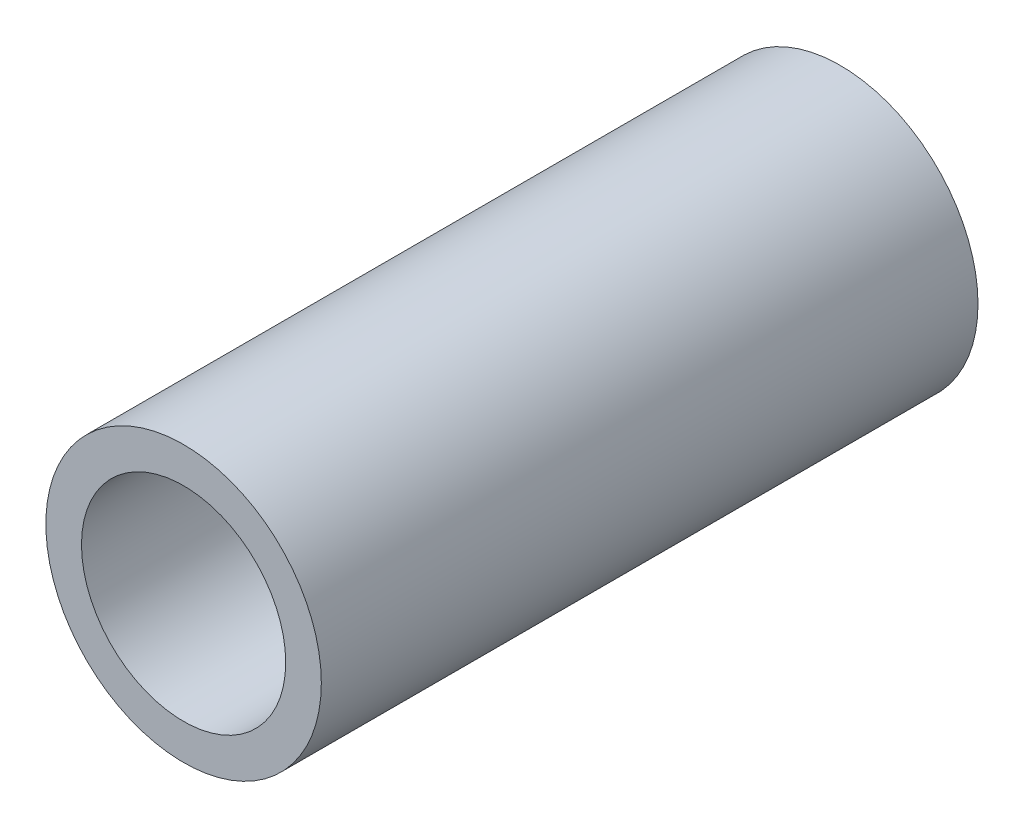
SolidWorks part; units mm, degrees
material "PVC Rigid"
ref_plane "Front Plane" through (0, 0, 0) normal (0, 0, 1) x (1, 0, 0)
ref_plane "Top Plane" through (0, 0, 0) normal (0, 1, 0) x (1, 0, 0)
ref_plane "Right Plane" through (0, 0, 0) normal (1, 0, 0) x (0, 0, -1)
sketch "Sketch1" plane through (0, 0, 0) normal (0, 0, 1) x (1, 0, 0)
  circle A0 centre (0, 0) radius 10.6553
  circle A2 centre (0, 0) radius 7.8994
  dimension "D1" = 21.3106
  dimension "D2" = 15.7988
extrude "Boss-Extrude1" add sketch "Sketch1" along normal blind 50.8
